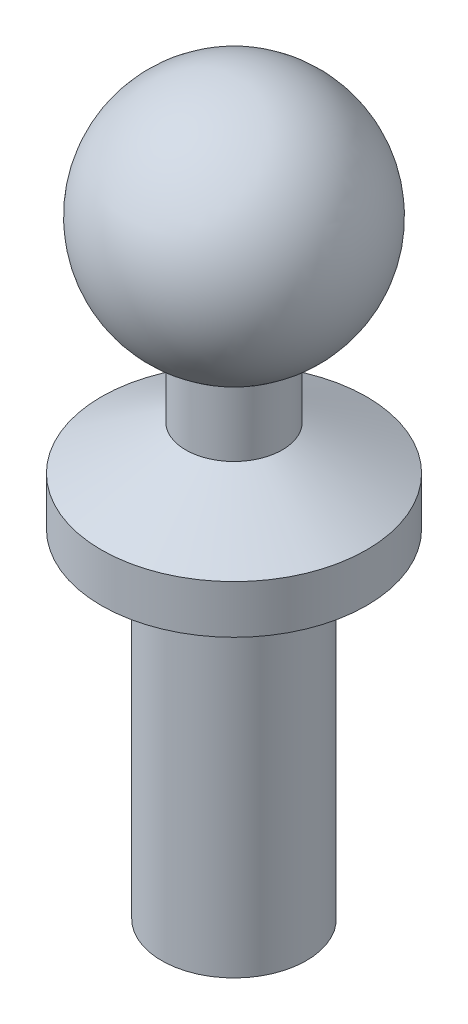
SolidWorks part; units mm, degrees
ref_plane "Front Plane" through (0, 0, 0) normal (0, 0, 1) x (1, 0, 0)
ref_plane "Top Plane" through (0, 0, 0) normal (0, 1, 0) x (1, 0, 0)
ref_plane "Right Plane" through (0, 0, 0) normal (1, 0, 0) x (0, 0, -1)
sketch "Sketch1" plane through (0, 0, 0) normal (0, 0, 1) x (1, 0, 0)
  line L0 (0, 0) -> (0, 15.11) construction
  line L1 (1.5, 0) -> (1.5, 7)
  line L2 (1.5, 7) -> (2.75, 7)
  line L3 (2.75, 7) -> (2.75, 8)
  line L4 (2.75, 8) -> (1, 8.9187)
  line L5 (1, 8.9187) -> (1, 10.3187)
  line L6 (0, 0) -> (1.5, 0)
  line L7 (0, 0) -> (0, 15.11)
  arc A0 (1, 10.3187) -> (0, 15.11) centre (0, 12.61) ccw
  dimension "D1" = 15.11
  dimension "D6" = 5
  dimension "D2" = 7
  dimension "D3" = 1
  dimension "D4" = 1.5
  dimension "D5" = 1.4
  dimension "D7" = 2
  dimension "D8" = 5.5
revolve "Revolve1" add sketch "Sketch1" angle 360 about L0
